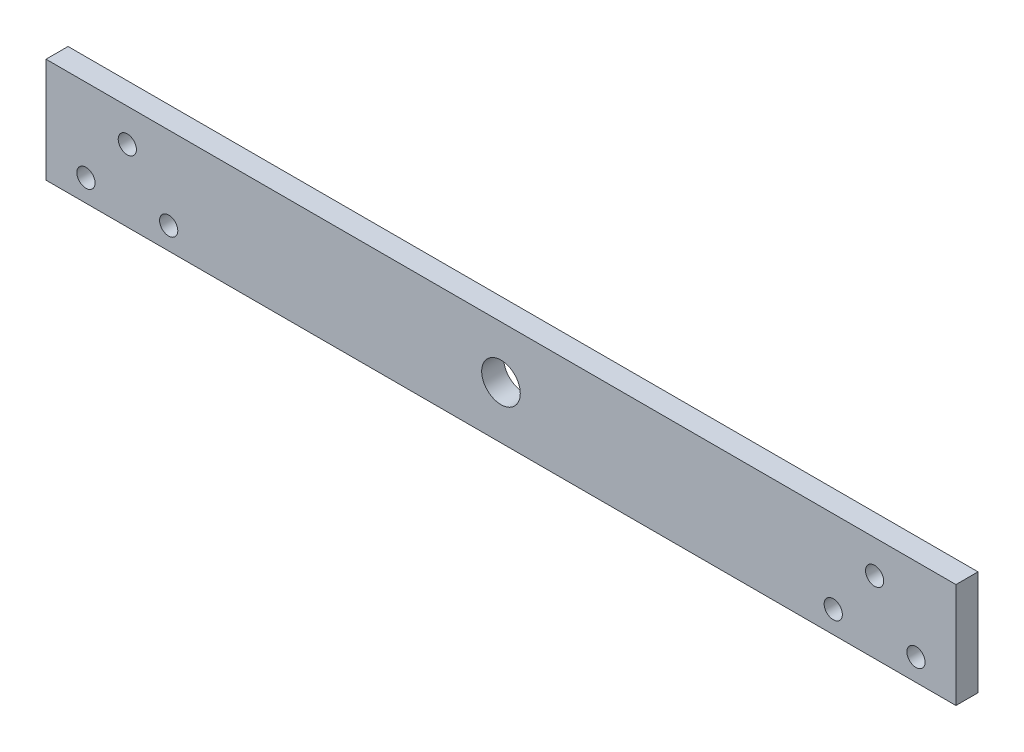
SolidWorks part; units mm, degrees
ref_plane "Front Plane" through (0, 0, 0) normal (0, 0, 1) x (1, 0, 0)
ref_plane "Top Plane" through (0, 0, 0) normal (0, 1, 0) x (1, 0, 0)
ref_plane "Right Plane" through (0, 0, 0) normal (1, 0, 0) x (0, 0, -1)
sketch "Sketch2" plane through (0, 0, 0) normal (0, 0, 1) x (1, 0, 0)
  line L1 (-165, 19) -> (165, 19)
  line L2 (-165, 19) -> (-165, -19)
  line L3 (-165, -19) -> (165, -19)
  line L4 (165, 19) -> (165, -19)
  point P4 (0, 19)
  point P6 (165, 0)
  dimension "D1" = 330
  dimension "D2" = 38
extrude "Boss-Extrude1" add sketch "Sketch2" along normal blind 8
sketch "Sketch3" plane through (0, 0, 8) normal (0, 0, 1) x (1, 0, 0)
  circle A0 centre (0, 0) radius 7
  dimension "D1" = 14
extrude "Cut-Extrude1" cut sketch "Sketch3" against normal through all
sketch "Sketch4" plane through (0, 0, 8) normal (0, 0, 1) x (1, 0, 0)
  line L0 (-135.5083, 7) -> (-150.5083, -11) construction
  line L1 (-150.5083, -11) -> (-120.5083, -11) construction
  line L2 (-120.5083, -11) -> (-135.5083, 7) construction
  line L3 (-165, -19) -> (165, -19) construction
  circle A0 centre (-135.5083, 7) radius 3.3
  circle A1 centre (-120.5083, -11) radius 3.3
  circle A2 centre (-150.5083, -11) radius 3.3
  point P4 (-135.5083, -11)
  dimension "D4" = 6.6
  dimension "D5" = 6.6
  dimension "D6" = 6.6
  dimension "D1" = 30
  dimension "D2" = 18
  dimension "D3" = 8
extrude "Cut-Extrude2" cut sketch "Sketch4" against normal through all
mirror "Mirror1" about plane through (0, 0, 0) normal (1, 0, 0) of "Cut-Extrude2"
